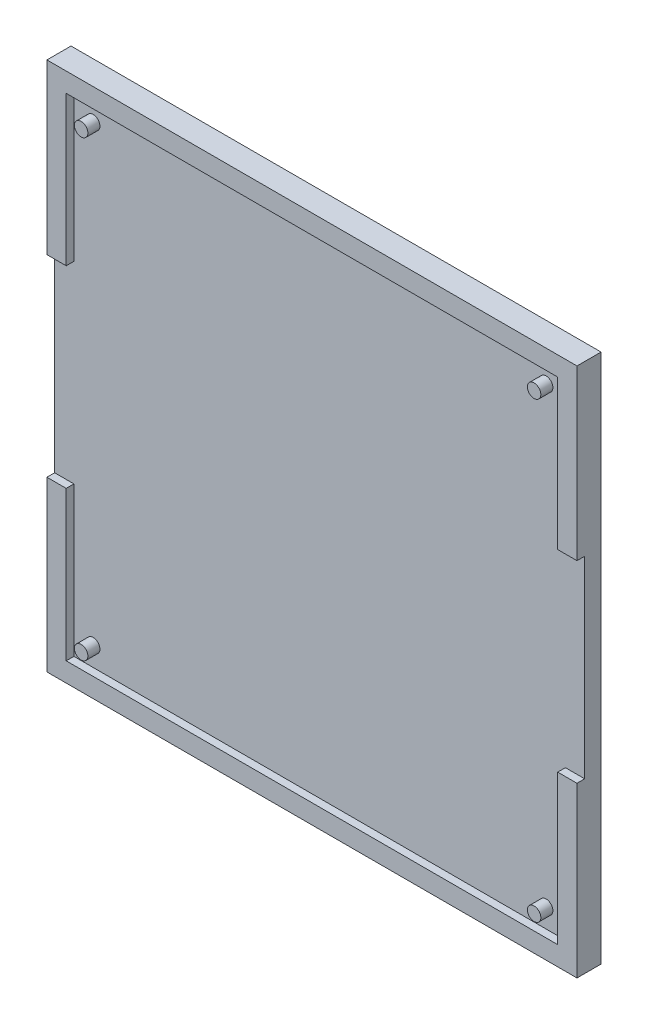
SolidWorks part; units mm, degrees
ref_plane "Front Plane" through (0, 0, 0) normal (0, 0, 1) x (1, 0, 0)
ref_plane "Top Plane" through (0, 0, 0) normal (0, 1, 0) x (1, 0, 0)
ref_plane "Right Plane" through (0, 0, 0) normal (1, 0, 0) x (0, 0, -1)
sketch "Sketch1" plane through (0, 0, 0) normal (0, 0, -1) x (1, 0, 0)
  line L1 (0, 0) -> (110, 0)
  line L2 (0, 0) -> (0, 110)
  line L3 (0, 110) -> (110, 110)
  line L4 (110, 0) -> (110, 110)
  dimension "D1" = 110
  dimension "D2" = 110
extrude "Boss-Extrude1" add sketch "Sketch1" against normal blind 5
sketch "Sketch3" plane through (0, 0, 5) normal (0, 0, 1) x (-1, 0, 0)
  line L1 (-106, 106) -> (-4, 106)
  line L2 (-106, 106) -> (-106, 4)
  line L3 (-106, 4) -> (-4, 4)
  line L4 (-4, 106) -> (-4, 4)
  line L5 (0, 0) -> (-110, 0) construction
  line L6 (-110, 0) -> (-110, 110) construction
  dimension "D1" = 102
  dimension "D2" = 102
  dimension "D3" = 4
  dimension "D4" = 4
extrude "Cut-Extrude1" cut sketch "Sketch3" against normal blind 1.6
sketch "Sketch4" plane through (0, 0, 3.4) normal (0, 0, 1) x (-1, 0, 0)
  line L0 (-4, 106) -> (-106, 106) construction
  line L2 (-4, 4) -> (-4, 106) construction
  line L3 (-106, 106) -> (-106, 4) construction
  circle A0 centre (-102, 102) radius 1.4
  circle A1 centre (-8, 102) radius 1.4
  circle A2 centre (-102, 8) radius 1.4
  circle A3 centre (-8, 8) radius 1.4
  dimension "D1" = 2.8
  dimension "D2" = 2.8
  dimension "D4" = 2.8
  dimension "D6" = 2.8
  dimension "D3" = 94
  dimension "D5" = 94
  dimension "D7" = 94
  dimension "D8" = 94
  dimension "D9" = 4
  dimension "D10" = 4
  dimension "D11" = 4
  dimension "D12" = 4
extrude "Boss-Extrude3" add sketch "Sketch4" along normal blind 2.5
sketch "Sketch11" plane through (0, 0, 5) normal (0, 0, 1) x (-1, 0, 0)
  line L0 (-106, 106) -> (-106, 4) construction
  line L1 (-106, 75) -> (-111, 75)
  line L2 (-106, 75) -> (-106, 35)
  line L3 (-106, 35) -> (-111, 35)
  line L4 (-111, 75) -> (-111, 35)
  line L5 (-106, 4) -> (-4, 4) construction
  line L8 (-4, 4) -> (-4, 106) construction
  line L9 (-4, 35) -> (1, 35)
  line L10 (-4, 35) -> (-4, 75)
  line L11 (-4, 75) -> (1, 75)
  line L12 (1, 35) -> (1, 75)
  line L13 (-4, 106) -> (-106, 106) construction
  dimension "D1" = 40
  dimension "D2" = 31
  dimension "D3" = 5
  dimension "D4" = 5
  dimension "D5" = 31
  dimension "D6" = 40
extrude "Cut-Extrude3" cut sketch "Sketch11" against normal blind 1.6
